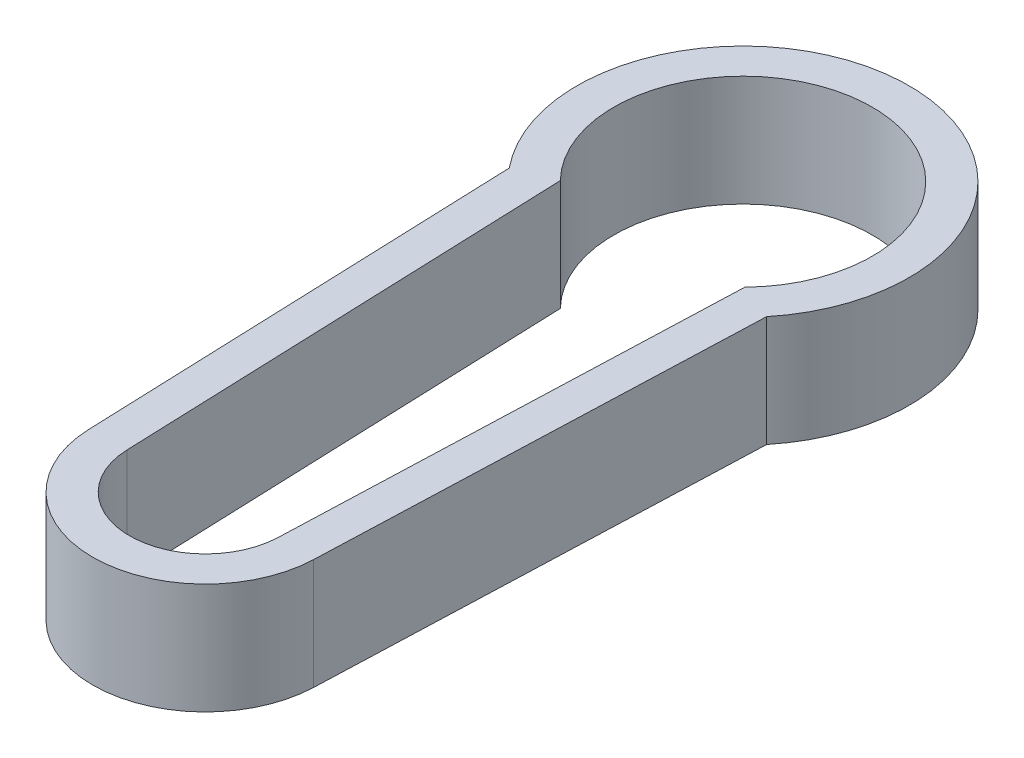
SolidWorks part; units mm, degrees
ref_plane "前基準面" through (0, 0, 0) normal (0, 0, 1) x (1, 0, 0)
ref_plane "上基準面" through (0, 0, 0) normal (0, 1, 0) x (1, 0, 0)
ref_plane "右基準面" through (0, 0, 0) normal (1, 0, 0) x (0, 0, -1)
sketch "草圖1" plane through (0, 0, 0) normal (0, 1, 0) x (1, 0, 0)
  line L0 (-2.5, -2.4495) -> (-2.05, -14.6412)
  line L1 (-3.4861, -2.8456) -> (-3.0493, -14.6781)
  line L2 (0, -55) -> (0, 55) construction
  line L4 (2.5, -2.4495) -> (2.05, -14.6412)
  line L6 (3.4861, -2.8456) -> (3.0493, -14.6781)
  arc A0 (2.5, -2.4495) -> (-2.5, -2.4495) centre (0, 0) ccw
  arc A3 (-2.05, -14.6412) -> (2.05, -14.6412) centre (0, -14.5655) ccw
  arc A4 (-3.0493, -14.6781) -> (3.0493, -14.6781) centre (0, -14.5655) ccw
  arc A5 (3.4861, -2.8456) -> (-3.4861, -2.8456) centre (0, 0) ccw
  dimension "D1" = 7
  dimension "D2" = 5
  dimension "D3" = 12.2
  dimension "D4" = 12.2
  dimension "D5" = 4.1
  dimension "D6" = 2.05
  dimension "D7" = 1
  dimension "D8" = 2.5
extrude "填料-伸長1" add sketch "草圖1" along normal blind 3
